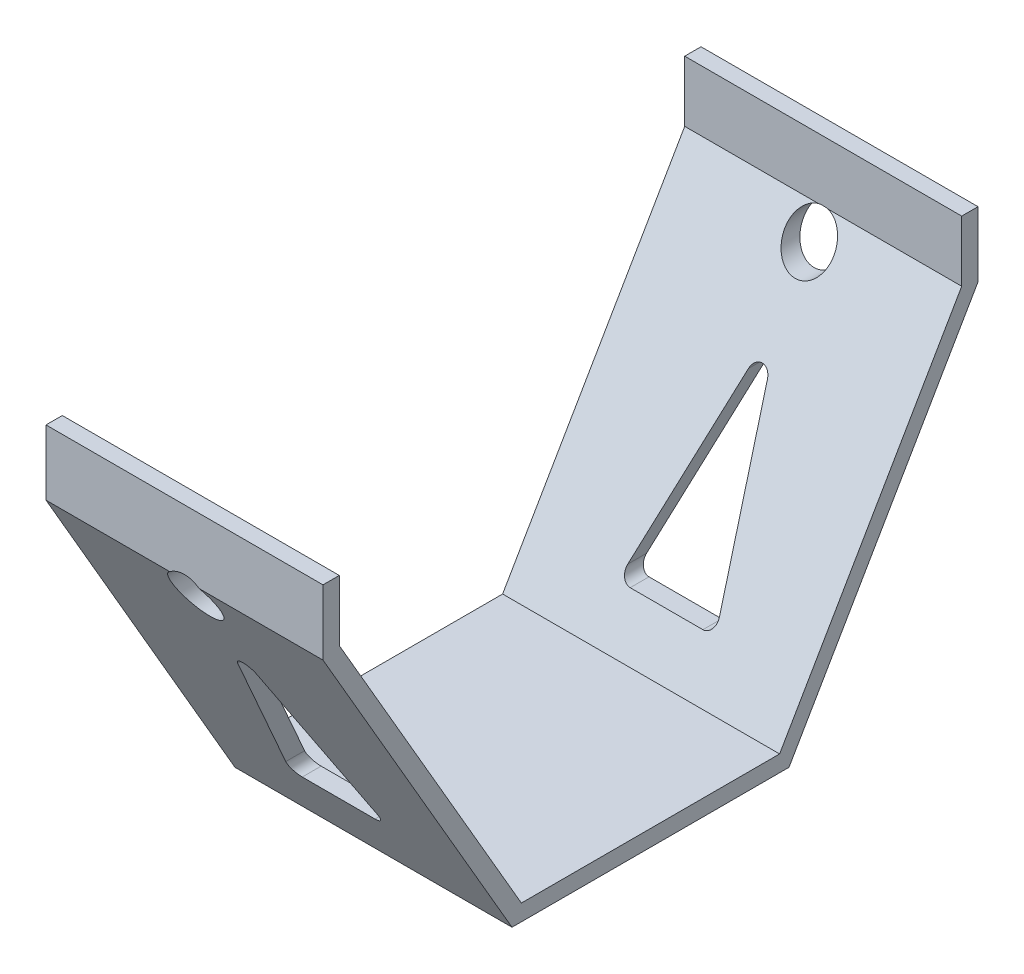
SolidWorks part; units mm, degrees
ref_plane "前视基准面" through (0, 0, 0) normal (0, 0, 1) x (1, 0, 0)
ref_plane "上视基准面" through (0, 0, 0) normal (0, 1, 0) x (1, 0, 0)
ref_plane "右视基准面" through (0, 0, 0) normal (1, 0, 0) x (0, 0, -1)
sketch "草图1" plane through (0, 0, 0) normal (1, 0, 0) x (0, 0, -1)
  line L0 (-42.5, 0) -> (42.5, 0)
  line L1 (42.5, 0) -> (100.5, 120) construction
  line L2 (100.5, 120) -> (-100.5, 120)
  line L3 (-100.5, 120) -> (-42.5, 0) construction
  line L4 (0, 0) -> (0, 120) construction
  line L5 (-100.5, 120) -> (-100.5, 100)
  line L6 (-100.5, 100) -> (-42.5, 0)
  line L7 (100.5, 120) -> (100.5, 100)
  line L8 (100.5, 100) -> (42.5, 0)
  line L9 (-39.6199, 5) -> (39.6199, 5)
  line L10 (95.5, 101.3451) -> (39.6199, 5)
  line L11 (95.5, 115) -> (95.5, 101.3451)
  line L12 (95.5, 115) -> (-95.5, 115)
  line L13 (-95.5, 115) -> (-95.5, 101.3451)
  line L14 (-95.5, 101.3451) -> (-39.6199, 5)
  line L15 (-95.5, 115) -> (-95.5, 120)
  line L16 (95.5, 115) -> (95.5, 120)
  point P4 (0, 0)
  dimension "D1" = 201
  dimension "D2" = 120
  dimension "D3" = 85
  dimension "D4" = 20
  dimension "D5" = 5
extrude "凸台-拉伸1" add sketch "草图1" along normal mid plane 85 contours L16 L11 L10 L9 L14 L13 L15 L2 L5 L6 L0 L8 L7
sketch "草图3" plane through (0, 0, 0) normal (0, -1, 0) x (1, 0, 0)
  circle A0 centre (0, 0) radius 15
  dimension "D1" = 30
extrude "凸台-拉伸2" add sketch "草图3" along normal blind 22
sketch "草图4" plane through (0, 0, 0) normal (0, 0, 1) x (1, 0, 0)
  line L0 (0, 0) -> (0, 78.4509) construction
  line L1 (0, 78.4509) -> (-15, 18.4509)
  line L2 (-15, 18.4509) -> (15, 18.4509)
  line L3 (0, 78.4509) -> (15, 18.4509)
  point P6 (0, 18.4509)
  dimension "D1" = 60
  dimension "D2" = 30
extrude "切除-拉伸1" cut sketch "草图4" against normal through all and the other way through all
fillet "圆角1" radius 3 6 edges at (0, 78.4509, -85.1114) (-15, 18.4509, -50.3114) (15, 18.4509, -50.3114) (15, 18.4509, 50.3114) (-15, 18.4509, 50.3114) (0, 78.4509, 85.1114)
sketch "草图5" plane through (0, 0, 100.5) normal (0, 0, 1) x (1, 0, 0)
  line L0 (42.5, 0) -> (-42.5, 0) construction
  circle A0 centre (0, 94) radius 7.5
  dimension "D2" = 15
  dimension "D1" = 94
extrude "切除-拉伸2" cut sketch "草图5" against normal through all
